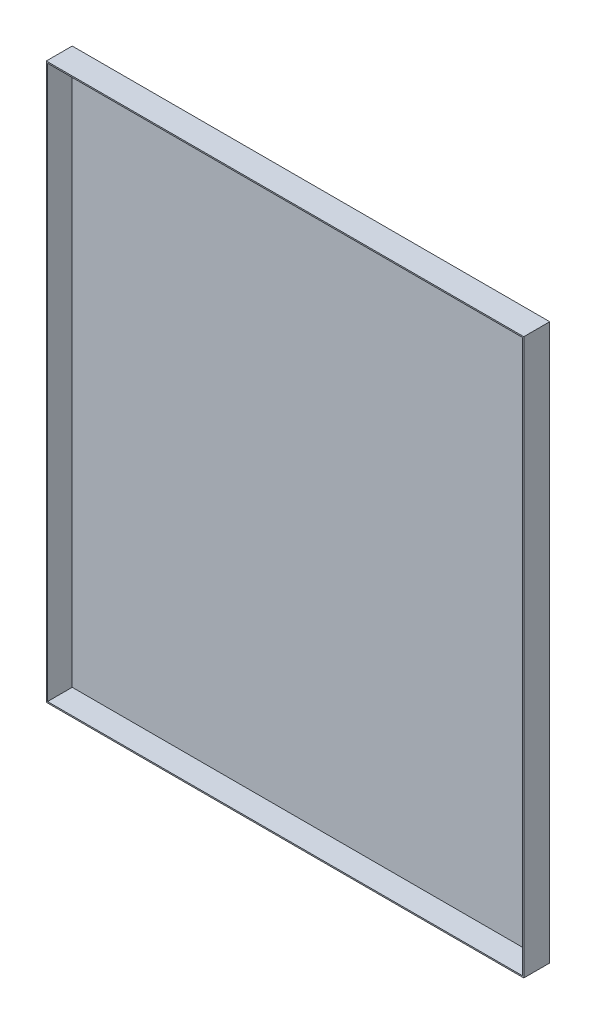
SolidWorks part; units mm, degrees
ref_plane "前视基准面" through (0, 0, 0) normal (0, 0, 1) x (1, 0, 0)
ref_plane "上视基准面" through (0, 0, 0) normal (0, 1, 0) x (1, 0, 0)
ref_plane "右视基准面" through (0, 0, 0) normal (1, 0, 0) x (0, 0, -1)
sketch "草图1" plane through (0, 0, 0) normal (0, 0, 1) x (1, 0, 0)
  line L1 (-184, 214) -> (184, 214)
  line L2 (-184, 214) -> (-184, -214)
  line L3 (-184, -214) -> (184, -214)
  line L4 (184, 214) -> (184, -214)
  line L5 (-184, 214) -> (184, -214) construction
  line L6 (-184, -214) -> (184, 214) construction
  point P0 (0, 0)
  dimension "D1" = 368
  dimension "D2" = 428
extrude "凸台-拉伸1" add sketch "草图1" along normal blind 20
shell "抽壳1" thickness 1
